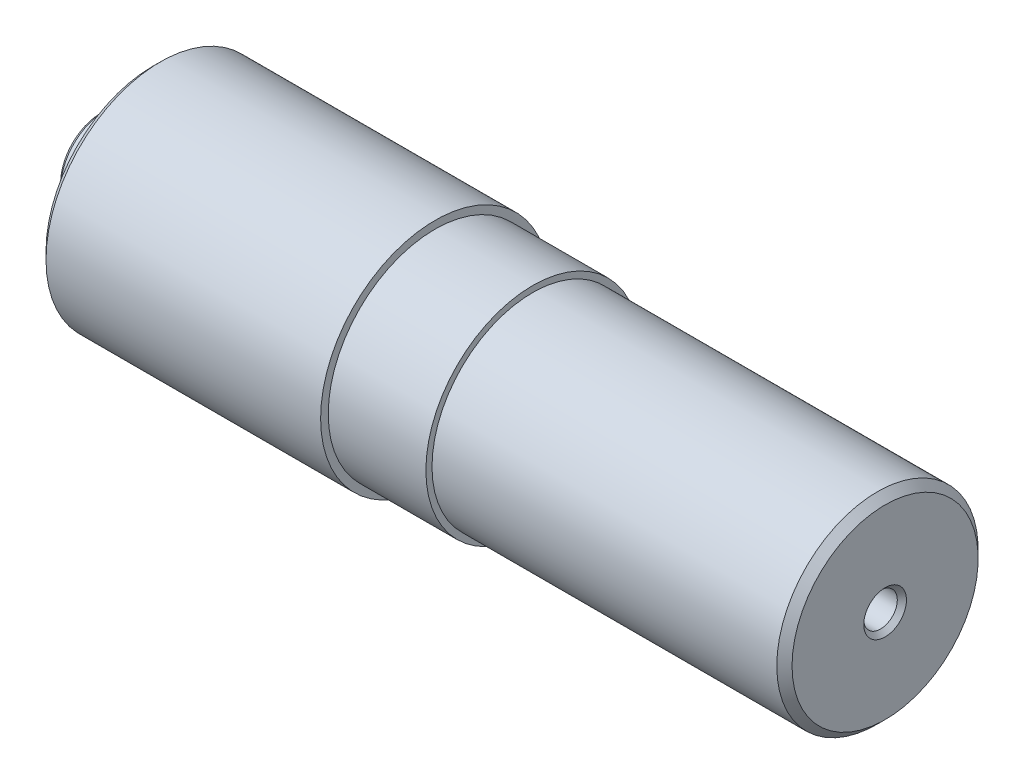
SolidWorks part; units mm, degrees
ref_plane "Front Plane" through (0, 0, 0) normal (0, 0, 1) x (1, 0, 0)
ref_plane "Top Plane" through (0, 0, 0) normal (0, 1, 0) x (1, 0, 0)
ref_plane "Right Plane" through (0, 0, 0) normal (1, 0, 0) x (0, 0, -1)
sketch "Sketch1" plane through (0, 0, 0) normal (0, 0, 1) x (1, 0, 0)
  line L0 (0, 0) -> (257, 0) construction
  line L1 (0, 0) -> (0, 14.7)
  line L2 (0, 14.7) -> (17, 14.7)
  line L3 (17, 14.7) -> (17, 37.5)
  line L4 (17, 37.5) -> (109.5, 37.5)
  line L5 (109.5, 37.5) -> (109.5, 35)
  line L6 (109.5, 35) -> (128.5, 35)
  line L7 (128.5, 35) -> (141.5, 35)
  line L8 (141.5, 35) -> (141.5, 33)
  line L9 (141.5, 33) -> (257, 33)
  line L10 (257, 33) -> (257, 0)
  line L11 (0, 0) -> (257, 0)
  dimension "D1" = 257
  dimension "D2" = 14.7
  dimension "D3" = 37.5
  dimension "D4" = 35
  dimension "D5" = 33
  dimension "D6" = 17
  dimension "D7" = 92.5
  dimension "D8" = 19
  dimension "D9" = 13
  dimension "D10" = 115.5
revolve "Revolve1" add sketch "Sketch1" angle 360 about L0
chamfer "Chamfer1" distance 2.5 angle 45 2 edges at (257, 0, 33) (17, 0, 37.5)
chamfer "Chamfer2" distance 1.5 angle 45 1 edges at (0, 0, 14.7)
hole_wizard "CSK for M10 Countersunk Flat Head Screw1" positions "Sketch3" profile "Sketch4" countersink size "M10" standard "ISO"
sketch "Sketch3" plane through (0, 0, 0) normal (-1, 0, 0) x (0, 0, 1)
  point P0 (0, 0)
sketch "Sketch4" plane through (0, 0, 0) normal (0, 1, 0) x (0, 0, 1)
  line L0 (0, 0) -> (0, 14)
  line L1 (0, 14) -> (5.5, 10.6953)
  line L2 (5.5, 10.6953) -> (5.5, 1.5)
  line L3 (5.5, 1.5) -> (7, 0)
  line L5 (7, 0) -> (0, 0)
  line L6 (-5.5, 1.5) -> (-7, 0) construction
  line L10 (0, 14) -> (-5.5, 10.6953) construction
  line L11 (0, -6.35) -> (0, 107.95) construction
  dimension "Hole Dia." = 11
  dimension "Hole Depth" = 14
  dimension "Near C'Sink Dia." = 14
  dimension "Near C'Sink Angle" = 90
  dimension "Drill Angle" = 118
hole_wizard "CSK for M10 Countersunk Flat Head Screw2" positions "Sketch5" profile "Sketch6" countersink size "M10" standard "ISO"
sketch "Sketch5" plane through (257, 0, 0) normal (1, 0, 0) x (0, 0, -1)
  point P0 (0, 0)
sketch "Sketch6" plane through (257, 0, 0) normal (0, 1, 0) x (0, 0, -1)
  line L0 (0, 0) -> (0, 14)
  line L1 (0, 14) -> (5.5, 10.6953)
  line L2 (5.5, 10.6953) -> (5.5, 1.5)
  line L3 (5.5, 1.5) -> (7, 0)
  line L5 (7, 0) -> (0, 0)
  line L6 (-5.5, 1.5) -> (-7, 0) construction
  line L10 (0, 14) -> (-5.5, 10.6953) construction
  line L11 (0, -6.35) -> (0, 107.95) construction
  dimension "Hole Dia." = 11
  dimension "Hole Depth" = 14
  dimension "Near C'Sink Dia." = 14
  dimension "Near C'Sink Angle" = 90
  dimension "Drill Angle" = 118
